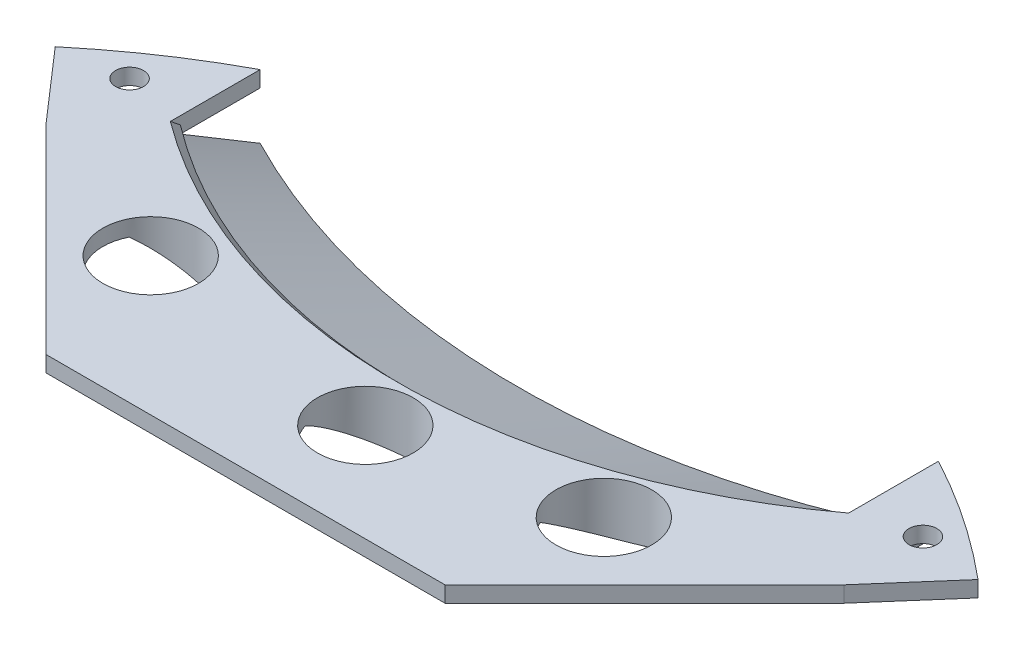
SolidWorks part; units mm, degrees
ref_plane "Front Plane" through (0, 0, 0) normal (0, 0, 1) x (1, 0, 0)
ref_plane "Top Plane" through (0, 0, 0) normal (0, 1, 0) x (1, 0, 0)
ref_plane "Right Plane" through (0, 0, 0) normal (1, 0, 0) x (0, 0, -1)
sketch "Sketch1" plane through (0, 0, 0) normal (0, 1, 0) x (1, 0, 0)
  circle A0 centre (0, 0) radius 90
extrude "Boss-Extrude1" add sketch "Sketch1" along normal blind 2
sketch "Sketch4" plane through (0, 2, 0) normal (0, 1, 0) x (1, 0, 0)
  line L0 (0, 90) -> (0, 55) construction
  line L1 (-42.5, 79.3332) -> (-42.5, 69.3332)
  line L2 (42.5, 79.3332) -> (42.5, 69.3332)
  line L3 (-42.5, 79.3332) -> (-42.5, 105.8098)
  line L4 (-42.5, 105.8098) -> (42.5, 105.8098)
  line L5 (42.5, 105.8098) -> (42.5, 79.3332)
  circle A0 centre (0, 0) radius 90 construction
  arc A1 (-42.5, 69.3332) -> (42.5, 69.3332) centre (0, 125.1761) ccw
  circle A5 centre (0, 0) radius 90 construction
  dimension "D1" = 35
  dimension "D2" = 42.5
  dimension "D3" = 42.5
  dimension "D4" = 10
  dimension "D5" = 10
extrude "Cut-Extrude2" cut sketch "Sketch4" against normal through all
sketch "Sketch9" plane through (0, 2, 0) normal (0, 1, 0) x (1, 0, 0)
  circle A0 centre (-49.7064, 70.1803) radius 1.75
  arc A1 (-42.5, 79.3332) -> (42.5, 79.3332) centre (0, 0) ccw construction
  dimension "D2" = 3.5
  dimension "D1" = 86
extrude "Cut-Extrude7" cut sketch "Sketch9" against normal through all
mirror "Mirror1" about plane through (0, 0, 0) normal (1, 0, 0) of "Cut-Extrude7"
sketch "Sketch10" plane through (0, 0, 0) normal (0, -1, 0) x (1, 0, 0)
  line L0 (57.8174, -68.9721) -> (50, -60)
  line L1 (50, -60) -> (25, -35)
  line L2 (25, -35) -> (-25, -35)
  line L3 (-25, -35) -> (-50, -60)
  line L4 (-50, -60) -> (-57.8174, -68.9721)
  line L5 (0, 0) -> (0, -35) construction
  arc A0 (42.5, -79.3332) -> (-42.5, -79.3332) centre (0, 0) ccw construction
  dimension "D1" = 35
  dimension "D2" = 25
  dimension "D3" = 25
  dimension "D5" = 25
  dimension "D7" = 25
  dimension "D8" = 11.9
  dimension "D9" = 11.9
extrude "Cut-Extrude8" cut sketch "Sketch10" along direction (0, 1, 0) on the side against the normal through all and the other way through all flip side to cut
ref_plane "Plane1" through (0, -6, 0) normal (0, 1, 0) x (1, 0, 0)
sketch "Sketch15" plane through (0, -6, 0) normal (0, 1, 0) x (1, 0, 0)
  line L0 (-42.5, 69.3332) -> (-42.5, 79.3332)
  line L1 (42.5, 69.3332) -> (42.5, 79.3332)
  arc A0 (-42.5, 79.3332) -> (42.5, 79.3332) centre (0, 161.8761) ccw
  arc A1 (-42.5, 69.3332) -> (42.5, 69.3332) centre (0, 125.1761) ccw
sketch "Sketch16" plane through (0, 0, 0) normal (0, -1, 0) x (1, 0, 0)
  line L0 (-45.9485, -63.852) -> (-42.5, -69.3332)
  line L1 (44.152, -63.852) -> (42.5, -69.3332)
  arc A0 (-42.5, -69.3332) -> (42.5, -69.3332) centre (0, -125.1761) cw
  arc A1 (-45.9485, -63.852) -> (44.152, -63.852) centre (-0.8982, -109.7669) cw
loft "Loft1" add profiles "Sketch15", "Sketch16"
chamfer "Chamfer3" distance 1 angle 45 1 edges at (0, 2, -55)
sketch "Sketch17" plane through (0, 2, 0) normal (0, 1, 0) x (1, 0, 0)
  circle A0 centre (2.6977, 47.316) radius 6
  circle A1 centre (27.6286, 52.2741) radius 6
  circle A2 centre (-29.1519, 52.2741) radius 6
  point P6 (-25.2638, 53.7119)
  point P7 (-0.277, 49.2663)
  point P8 (-0.5478, 49.305)
  point P9 (23.8753, 53.7119)
  point P10 (-23.4347, 53.1053)
  point P11 (-22.864, 53.7119)
  point P12 (-25.9307, 51.9008)
  point P13 (1.6591, 47.4561)
  point P14 (26.3676, 52.2714)
  point P15 (27.9486, 52.4123)
  point P16 (2.6977, 47.316)
  point P17 (-28.8359, 53.3408)
  point P18 (-28.9496, 52.7724)
  point P19 (27.8309, 52.7724)
  point P20 (0, 0)
  point P21 (0, 0)
  dimension "D1" = 12
  dimension "D2" = 12
  dimension "D3" = 12
extrude "Cut-Extrude9" cut sketch "Sketch17" against normal through all
